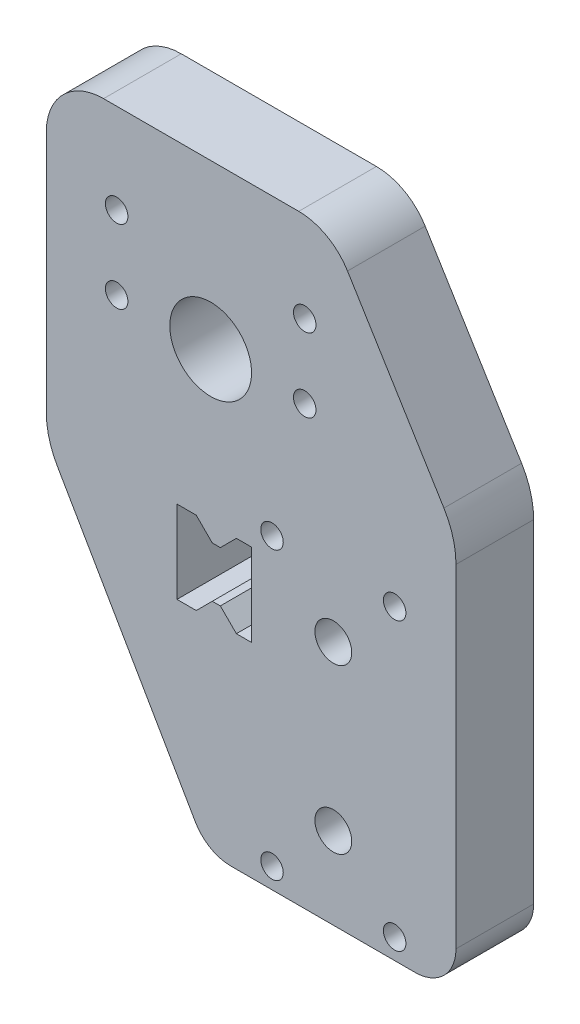
SolidWorks part; units mm, degrees
ref_plane "Front Plane" through (0, 0, 0) normal (0, 0, 1) x (1, 0, 0)
ref_plane "Top Plane" through (0, 0, 0) normal (0, 1, 0) x (1, 0, 0)
ref_plane "Right Plane" through (0, 0, 0) normal (1, 0, 0) x (0, 0, -1)
sketch "Sketch1" plane through (0, 0, 0) normal (0, 0, 1) x (1, 0, 0)
  line L0 (-130, 510) -> (13.8884, 510) construction
  line L1 (-170.2, 540.8246) -> (-129.3094, 470)
  line L2 (-116.2253, 607) -> (-90, 564.2553)
  line L15 (-90, 473) -> (-90, 564.2553)
  line L16 (-90, 473) -> (-90, 547) construction
  line L24 (-170.2, 540.8246) -> (-170.2, 607)
  line L25 (-170.2, 607) -> (-116.2253, 607)
  line L183 (-129.3094, 470) -> (-93, 470)
  arc A1 (-113.8, 602.2) -> (-116.8, 605.2) centre (-116.8, 602.2) ccw construction
  arc A13 (-90, 473) -> (-93, 470) centre (-93, 473) cw
extrude "Boss-Extrude1" add sketch "Sketch1" along normal blind 19
fillet "Fillet1" radius 10 3 edges at (-129.3094, 470, 9.5) (-170.2, 540.8246, 9.5) (-90, 564.2553, 9.5)
sketch "Sketch2" plane through (0, 0, 19) normal (0, 0, 1) x (1, 0, 0)
  circle A0 centre (-139, 577) radius 20
  dimension "D1" = 40
hole_wizard "M5 Clearance Hole2" positions "Sketch5" profile "Sketch6" hole size "M5" standard "ISO" end condition through all
sketch "Sketch5" plane through (0, 0, 0) normal (0, 0, -1) x (-1, 0, 0)
  line L1 (117, 595) -> (117, 577)
  line L2 (117, 595) -> (163, 595)
  line L3 (163, 595) -> (163, 577)
  line L4 (117, 577) -> (163, 577)
  circle A1 centre (117, 595) radius 2.1
  point P2 (117, 595)
  point P4 (117, 577)
  point P6 (163, 577)
  point P8 (163, 595)
  dimension "D1" = 18
  dimension "D2" = 46
  dimension "D3" = 46
  dimension "D4" = 18
sketch "Sketch6" plane through (-117, 595, 0) normal (1, 0, 0) x (0, 1, 0)
  line L0 (0, 0) -> (0, 19)
  line L1 (0, 19) -> (2.75, 19)
  line L2 (2.75, 19) -> (2.75, 0)
  line L5 (2.75, 0) -> (0, 0)
  line L11 (0, -6.35) -> (0, 107.95) construction
  dimension "Thru Hole Dia." = 5.5
  dimension "Thru Hole Depth" = 19
hole_wizard "M5 Clearance Hole1" positions "Sketch7" profile "Sketch8" hole size "M5" standard "ISO" end condition through all
sketch "Sketch7" plane through (0, 0, 19) normal (0, 0, 1) x (1, 0, 0)
  point P0 (-95, 545)
  point P2 (-125, 545)
  point P4 (-125, 475)
  point P6 (-95, 475)
  point P8 (-110, 490)
  point P10 (-110, 530)
sketch "Sketch8" plane through (-95, 545, 19) normal (1, 0, 0) x (0, -1, 0)
  line L0 (0, 0) -> (0, 19)
  line L1 (0, 19) -> (2.75, 19)
  line L2 (2.75, 19) -> (2.75, 0)
  line L5 (2.75, 0) -> (0, 0)
  line L11 (0, -6.35) -> (0, 107.95) construction
  dimension "Thru Hole Dia." = 5.5
  dimension "Thru Hole Depth" = 19
hole_wizard "Tap Drill for M5 Tap2" [suppressed] positions "Sketch9" profile "Sketch10" hole size "M5" standard "ISO"
sketch "Sketch9" plane through (0, 0, 19) normal (0, 0, 1) x (1, 0, 0)
  point P0 (-163.57, 553.43)
  point P2 (-163.57, 600.57)
  point P4 (-116.43, 553.43)
  point P6 (-116.43, 600.57)
sketch "Sketch10" plane through (-163.57, 553.43, 19) normal (1, 0, 0) x (0, -1, 0)
  line L0 (0, 0) -> (0, 19)
  line L1 (0, 19) -> (2.1, 19)
  line L2 (2.1, 19) -> (2.1, 0)
  line L5 (2.1, 0) -> (0, 0)
  line L11 (0, -6.35) -> (0, 107.95) construction
  dimension "Thru Hole Dia." = 4.2
  dimension "Thru Hole Depth" = 19
fillet "Fillet2" radius 4 2 edges at (-116.2253, 607, 9.5) (-170.2, 607, 9.5)
sketch "Sketch11" plane through (0, 0, 19) normal (0, 0, 1) x (1, 0, 0)
  line L6 (-135.0829, 470) -> (-90, 470)
  line L7 (-80, 480) -> (-80, 561.4321)
  line L8 (-82.9528, 571.8912) -> (-106.531, 610.3213)
  line L9 (-118.464, 617) -> (-166.2, 617)
  line L10 (-180.2, 603) -> (-180.2, 543.5041)
  line L11 (-177.5205, 533.5041) -> (-143.7432, 475)
  line L12 (-135.0829, 470) -> (-90, 470)
  line L13 (-80, 480) -> (-80, 561.4321)
  line L14 (-82.9528, 571.8912) -> (-106.531, 610.3213)
  line L15 (-118.464, 617) -> (-166.2, 617)
  line L16 (-180.2, 603) -> (-180.2, 543.5041)
  line L17 (-177.5205, 533.5041) -> (-143.7432, 475)
  line L18 (-91.4764, 566.6616) -> (-115.0546, 605.0918)
  line L19 (-118.464, 607) -> (-166.2, 607)
  line L20 (-170.2, 603) -> (-170.2, 543.5041)
  line L21 (-168.8603, 538.5041) -> (-132.1962, 475)
  line L22 (-123.5359, 470) -> (-93, 470)
  line L23 (-90, 473) -> (-90, 561.4321)
  line L24 (-91.4764, 566.6616) -> (-115.0546, 605.0918)
  line L25 (-118.464, 607) -> (-166.2, 607)
  line L26 (-170.2, 603) -> (-170.2, 543.5041)
  line L27 (-168.8603, 538.5041) -> (-132.1962, 475)
  line L28 (-123.5359, 470) -> (-93, 470)
  line L29 (-90, 473) -> (-90, 561.4321)
  arc A6 (-143.7432, 475) -> (-135.0829, 470) centre (-135.0829, 480) ccw
  arc A7 (-90, 470) -> (-80, 480) centre (-90, 480) ccw
  arc A8 (-80, 561.4321) -> (-82.9528, 571.8912) centre (-100, 561.4321) ccw
  arc A9 (-106.531, 610.3213) -> (-118.464, 617) centre (-118.464, 603) ccw
  arc A10 (-166.2, 617) -> (-180.2, 603) centre (-166.2, 603) ccw
  arc A11 (-180.2, 543.5041) -> (-177.5205, 533.5041) centre (-160.2, 543.5041) ccw
  arc A12 (-143.7432, 475) -> (-135.0829, 470) centre (-135.0829, 480) ccw
  arc A13 (-90, 470) -> (-80, 480) centre (-90, 480) ccw
  arc A14 (-80, 561.4321) -> (-82.9528, 571.8912) centre (-100, 561.4321) ccw
  arc A15 (-106.531, 610.3213) -> (-118.464, 617) centre (-118.464, 603) ccw
  arc A16 (-166.2, 617) -> (-180.2, 603) centre (-166.2, 603) ccw
  arc A17 (-180.2, 543.5041) -> (-177.5205, 533.5041) centre (-160.2, 543.5041) ccw
  arc A18 (-115.0546, 605.0918) -> (-118.464, 607) centre (-118.464, 603) ccw
  arc A19 (-166.2, 607) -> (-170.2, 603) centre (-166.2, 603) ccw
  arc A20 (-170.2, 543.5041) -> (-168.8603, 538.5041) centre (-160.2, 543.5041) ccw
  arc A21 (-132.1962, 475) -> (-123.5359, 470) centre (-123.5359, 480) ccw
  arc A22 (-93, 470) -> (-90, 473) centre (-93, 473) ccw
  arc A23 (-90, 561.4321) -> (-91.4764, 566.6616) centre (-100, 561.4321) ccw
  arc A24 (-115.0546, 605.0918) -> (-118.464, 607) centre (-118.464, 603) ccw
  arc A25 (-166.2, 607) -> (-170.2, 603) centre (-166.2, 603) ccw
  arc A26 (-170.2, 543.5041) -> (-168.8603, 538.5041) centre (-160.2, 543.5041) ccw
  arc A27 (-132.1962, 475) -> (-123.5359, 470) centre (-123.5359, 480) ccw
  arc A28 (-93, 470) -> (-90, 473) centre (-93, 473) ccw
  arc A29 (-90, 561.4321) -> (-91.4764, 566.6616) centre (-100, 561.4321) ccw
  dimension "D1" = 0
  dimension "D2" = 0
extrude "Boss-Extrude2" add sketch "Sketch11" against normal up to surface (19 mm away)
hole_wizard "M8 Clearance Hole1" positions "Sketch12" profile "Sketch13" hole size "M8" standard "ISO" end condition through all
sketch "Sketch12" plane through (0, 0, 19) normal (0, 0, 1) x (1, 0, 0)
  point P0 (-110, 530)
  point P3 (-110, 490)
sketch "Sketch13" plane through (-110, 530, 19) normal (1, 0, 0) x (0, -1, 0)
  line L0 (0, 0) -> (0, 19)
  line L1 (0, 19) -> (4.5, 19)
  line L2 (4.5, 19) -> (4.5, 0)
  line L5 (4.5, 0) -> (0, 0)
  line L11 (0, -6.35) -> (0, 107.95) construction
  dimension "Thru Hole Dia." = 9
  dimension "Thru Hole Depth" = 19
extrude "Cut-Extrude1" [suppressed] cut sketch "Sketch2" against normal through all
sketch "Sketch14" plane through (0, 0, 19) normal (0, 0, 1) x (1, 0, 0)
  line L0 (-177.5205, 533.5041) -> (-143.7432, 475)
  line L1 (-180.2, 603) -> (-180.2, 543.5041)
  line L2 (-118.464, 617) -> (-166.2, 617)
  line L3 (-82.9528, 571.8912) -> (-106.531, 610.3213)
  line L4 (-80, 480) -> (-80, 561.4321)
  line L5 (-135.0829, 470) -> (-90, 470)
  circle A0 centre (-110, 530) radius 4.5
  circle A1 centre (-95, 545) radius 2.75
  circle A2 centre (-165, 595) radius 2.1
  circle A3 centre (-165, 577) radius 2.1
  circle A4 centre (-119, 577) radius 2.1
  circle A5 centre (-119, 595) radius 2.1
  circle A6 centre (-95, 475) radius 2.75
  circle A7 centre (-125, 475) radius 2.75
  circle A8 centre (-125, 545) radius 2.75
  circle A9 centre (-110, 490) radius 4.5
  arc A10 (-180.2, 543.5041) -> (-177.5205, 533.5041) centre (-160.2, 543.5041) ccw
  arc A11 (-166.2, 617) -> (-180.2, 603) centre (-166.2, 603) ccw
  arc A12 (-106.531, 610.3213) -> (-118.464, 617) centre (-118.464, 603) ccw
  arc A13 (-80, 561.4321) -> (-82.9528, 571.8912) centre (-100, 561.4321) ccw
  arc A14 (-90, 470) -> (-80, 480) centre (-90, 480) ccw
  arc A15 (-143.7432, 475) -> (-135.0829, 470) centre (-135.0829, 480) ccw
sketch "Sketch15" plane through (0, 0, 0) normal (0, 0, 1) x (1, 0, 0)
  line L0 (-140, 595) -> (-140, 577) construction
  line L1 (-166.96, 579.2863) -> (-166.96, 574.7137)
  line L2 (-166.96, 574.7137) -> (-163, 572.4274)
  line L3 (-163, 572.4274) -> (-159.04, 574.7137)
  line L4 (-159.04, 574.7137) -> (-159.04, 579.2863)
  line L5 (-159.04, 579.2863) -> (-163, 581.5726)
  line L6 (-163, 581.5726) -> (-166.96, 579.2863)
  line L7 (-163, 577) -> (-117, 577) construction
  line L8 (-163, 577) -> (-163, 595) construction
  line L9 (-163, 595) -> (-117, 595) construction
  line L10 (-117, 577) -> (-117, 595) construction
  line L11 (-117, 586) -> (-163, 586) construction
  line L12 (-120.96, 579.2863) -> (-120.96, 574.7137)
  line L13 (-120.96, 574.7137) -> (-117, 572.4274)
  line L14 (-117, 572.4274) -> (-113.04, 574.7137)
  line L15 (-113.04, 574.7137) -> (-113.04, 579.2863)
  line L16 (-113.04, 579.2863) -> (-117, 581.5726)
  line L17 (-117, 581.5726) -> (-120.96, 579.2863)
  line L18 (-113.04, 592.7137) -> (-117, 590.4274)
  line L19 (-117, 590.4274) -> (-120.96, 592.7137)
  line L20 (-120.96, 592.7137) -> (-120.96, 597.2863)
  line L21 (-120.96, 597.2863) -> (-117, 599.5726)
  line L22 (-117, 599.5726) -> (-113.04, 597.2863)
  line L23 (-113.04, 597.2863) -> (-113.04, 592.7137)
  line L24 (-163, 590.4274) -> (-166.96, 592.7137)
  line L25 (-159.04, 592.7137) -> (-163, 590.4274)
  line L26 (-159.04, 597.2863) -> (-159.04, 592.7137)
  line L27 (-163, 599.5726) -> (-159.04, 597.2863)
  line L28 (-166.96, 597.2863) -> (-163, 599.5726)
  line L29 (-166.96, 592.7137) -> (-166.96, 597.2863)
  circle A0 centre (-163, 577) radius 3.96 construction
  point P18 (-140, 586)
  dimension "D1" = 7.92
  dimension "D2" = 2
extrude "Cut-Extrude2" cut sketch "Sketch15" along normal blind 4
sketch "Sketch16" plane through (0, 0, 19) normal (0, 0, -1) x (-1, 0, 0)
  circle A0 centre (140, 577) radius 10
  dimension "D1" = 20
extrude "Cut-Extrude3" cut sketch "Sketch16" along normal blind 5
sketch "Sketch18" plane through (0, 0, 19) normal (0, 0, 1) x (1, 0, 0)
  line L0 (-130, 540.1) -> (-133.7164, 540.1)
  line L1 (-133.7164, 540.1) -> (-137.6414, 536.175)
  line L2 (-137.6414, 536.175) -> (-139.6086, 536.175)
  line L3 (-139.6086, 536.175) -> (-143.5336, 540.1)
  line L4 (-143.5336, 540.1) -> (-148.25, 540.1)
  line L5 (-148.25, 540.1) -> (-148.25, 519.9)
  line L6 (-148.25, 519.9) -> (-143.5336, 519.9)
  line L7 (-143.5336, 519.9) -> (-139.6086, 523.825)
  line L8 (-139.6086, 523.825) -> (-137.6414, 523.825)
  line L9 (-137.6414, 523.825) -> (-133.7164, 519.9)
  line L10 (-133.7164, 519.9) -> (-130, 519.9)
  line L18 (-130, 520) -> (-130, 540) construction
  line L19 (-129.9, 540.1) -> (-133.7164, 540.1) construction
  line L20 (-133.7164, 519.9) -> (-129.9, 519.9) construction
  line L36 (-130, 540) -> (-133.675, 540) construction
  line L37 (-130, 519.9) -> (-130, 540.1)
  line L38 (-133.675, 520) -> (-130, 520) construction
  line L39 (-137.6, 523.925) -> (-133.675, 520) construction
  line L40 (-139.65, 523.925) -> (-137.6, 523.925) construction
  line L41 (-143.575, 520) -> (-139.65, 523.925) construction
  line L42 (-148.15, 520) -> (-143.575, 520) construction
  line L43 (-148.15, 540) -> (-148.15, 520) construction
  line L44 (-143.575, 540) -> (-148.15, 540) construction
  line L45 (-139.65, 536.075) -> (-143.575, 540) construction
  line L46 (-137.6, 536.075) -> (-139.65, 536.075) construction
  line L47 (-133.675, 540) -> (-137.6, 536.075) construction
  line L48 (-129.9, 519.9) -> (-129.9, 540.1) construction
  dimension "D1" = 0.1
extrude "Cut-Extrude4" cut sketch "Sketch18" against normal blind 20
sketch "Sketch19" plane through (0, 0, 14) normal (0, 0, 1) x (1, 0, 0)
  circle A0 centre (-140, 577) radius 10
extrude "Cut-Extrude5" cut sketch "Sketch19" against normal blind 20
